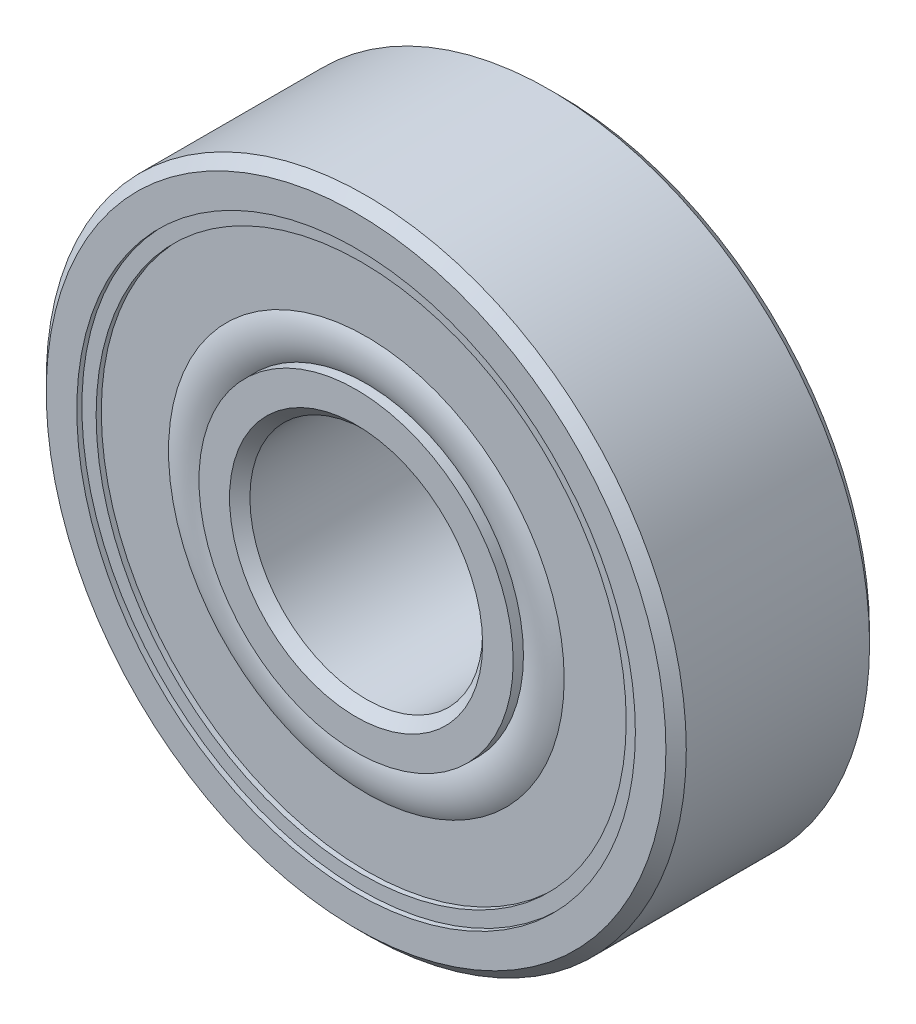
SolidWorks part; units mm, degrees
ref_plane "Front Plane" through (0, 0, 0) normal (0, 0, 1) x (1, 0, 0)
ref_plane "Top Plane" through (0, 0, 0) normal (0, 1, 0) x (1, 0, 0)
ref_plane "Right Plane" through (0, 0, 0) normal (1, 0, 0) x (0, 0, -1)
sketch "Sketch1" plane through (0, 0, 0) normal (0, 0, 1) x (1, 0, 0)
  circle A0 centre (0, 0) radius 11 construction
  circle A1 centre (0, 0) radius 4 construction
  dimension "OD" = 22
  dimension "ID" = 8
sketch "Sketch2" plane through (0, 0, 0) normal (1, 0, 0) x (0, 0, -1)
  line L0 (-3.5, 0) -> (3.5, 0) construction
  line L1 (0, 11) -> (0, -11) construction
  line L2 (3.15, 11) -> (-3.15, 11) construction
  line L3 (-3.15, 11) -> (-3.5, 10.65) construction
  line L4 (-3.5, 10.65) -> (-3.5, 9.6) construction
  line L5 (-3.5, 9.6) -> (-1.5556, 9.6) construction
  line L6 (3.5, 9.6) -> (1.5556, 9.6) construction
  line L7 (3.5, 10.65) -> (3.5, 9.6) construction
  line L8 (3.15, 11) -> (3.5, 10.65) construction
  line L9 (0, 11) -> (0, 7.5) construction
  line L10 (0, 7.5) -> (0, 4) construction
  line L11 (3.5, 7.5) -> (-3.5, 7.5) construction
  line L12 (-3.5, 4.35) -> (-3.5, 5.4) construction
  line L13 (-3.15, 4) -> (-3.5, 4.35) construction
  line L14 (3.15, 4) -> (-3.15, 4) construction
  line L15 (3.15, 4) -> (3.5, 4.35) construction
  line L16 (3.5, 4.35) -> (3.5, 5.4) construction
  line L17 (3.5, 5.4) -> (1.5556, 5.4) construction
  line L18 (-3.5, 5.4) -> (-1.5556, 5.4) construction
  line L19 (-3.5, 4) -> (-3.5, -4) construction
  line L20 (3.5, 11) -> (3.5, -11) construction
  arc A0 (-1.5556, 9.6) -> (1.5556, 9.6) centre (0, 7.5) cw construction
  arc A1 (-1.5556, 5.4) -> (1.5556, 5.4) centre (0, 7.5) ccw construction
  point P14 (0, 4)
  point P18 (0, 7.5)
  dimension "Approx. Ball Dia." = 5.2268
  dimension "D1" = 45
  dimension "D2" = 0.35
  dimension "D3" = 3.1111
  dimension "D4" = 2.1
  dimension "Width" = 7
  dimension "For Shaft Diameter" = 8
  dimension "For Housing ID" = 22
sketch "Sketch3" plane through (0, 0, 0) normal (1, 0, 0) x (0, 0, -1)
  line L0 (-3.5, 10.65) -> (-3.5, 9.6) construction
  line L1 (-3.15, 11) -> (-3.5, 10.65) construction
  line L2 (3.15, 11) -> (-3.15, 11) construction
  line L3 (3.15, 11) -> (3.5, 10.65) construction
  line L4 (3.5, 10.65) -> (3.5, 9.6) construction
  line L5 (3.5, 9.6) -> (1.5556, 9.6) construction
  line L6 (-3.5, 9.6) -> (-1.5556, 9.6) construction
  line L7 (-3.5, 10.65) -> (-3.5, 9.6)
  line L8 (-3.15, 11) -> (-3.5, 10.65)
  line L9 (3.15, 11) -> (-3.15, 11)
  line L10 (3.15, 11) -> (3.5, 10.65)
  line L11 (3.5, 10.65) -> (3.5, 9.6)
  line L12 (3.5, 9.6) -> (1.5556, 9.6)
  line L13 (-3.5, 9.6) -> (-1.5556, 9.6)
  line L14 (-3.5, 4.35) -> (-3.5, 5.4) construction
  line L15 (-3.15, 4) -> (-3.5, 4.35) construction
  line L16 (3.15, 4) -> (-3.15, 4) construction
  line L17 (3.15, 4) -> (3.5, 4.35) construction
  line L18 (3.5, 4.35) -> (3.5, 5.4) construction
  line L19 (3.5, 5.4) -> (1.5556, 5.4) construction
  line L20 (-3.5, 5.4) -> (-1.5556, 5.4) construction
  line L21 (-3.5, 4.35) -> (-3.5, 5.4)
  line L22 (-3.15, 4) -> (-3.5, 4.35)
  line L23 (3.15, 4) -> (-3.15, 4)
  line L24 (3.15, 4) -> (3.5, 4.35)
  line L25 (3.5, 4.35) -> (3.5, 5.4)
  line L26 (3.5, 5.4) -> (1.5556, 5.4)
  line L27 (-3.5, 5.4) -> (-1.5556, 5.4)
  arc A0 (1.5556, 9.6) -> (-1.5556, 9.6) centre (0, 7.5) ccw construction
  arc A1 (1.5556, 9.6) -> (-1.5556, 9.6) centre (0, 7.5) ccw
  arc A2 (-1.5556, 5.4) -> (1.5556, 5.4) centre (0, 7.5) ccw construction
  arc A3 (-1.5556, 5.4) -> (1.5556, 5.4) centre (0, 7.5) ccw
revolve "Revolve1" add sketch "Sketch3" angle 360 about L0
sketch "Sketch4" plane through (0, 0, 0) normal (1, 0, 0) x (0, 0, -1)
  line L0 (-2.6134, 7.5) -> (2.6134, 7.5)
  arc A2 (-2.6134, 7.5) -> (2.6134, 7.5) centre (0, 7.5) cw
  arc A3 (1.5556, 9.6) -> (-1.5556, 9.6) centre (0, 7.5) ccw construction
revolve "Revolve2" add sketch "Sketch4" angle 360 about L0
pattern_circular "CirPattern1" count 7 over 360 about axis through (0, 0, 0) along (0, 0, 1) of bodies 104
sketch "Sketch5" plane through (0, 0, 0) normal (1, 0, 0) x (0, 0, -1)
  line L0 (-3.5, 9.6) -> (-1.5556, 9.6) construction
  line L1 (-3.325, 9.6) -> (-2.6134, 9.6)
  line L2 (-3.325, 9.6) -> (-3.325, 9.11)
  line L3 (-3.325, 5.4) -> (-2.6134, 5.4) construction
  line L4 (-2.6134, 9.6) -> (-2.6134, 5.4)
  line L5 (0, 11) -> (0, 0) construction
  line L7 (-3.325, 9.11) -> (-3.1471, 9.11)
  line L8 (-3.1471, 9.11) -> (-3.1471, 6.8)
  line L9 (-3.1471, 6.8) -> (-3.325, 6.8) construction
  line L10 (-3.325, 6.8) -> (-3.325, 5.4) construction
  line L11 (3.15, 11) -> (-3.15, 11) construction
  line L12 (-3.15, 11) -> (-3.5, 10.65) construction
  line L13 (-3.5, 5.4) -> (-1.5556, 5.4) construction
  line L15 (-3.1471, 5.4) -> (-2.6134, 5.4)
  line L16 (3.325, 6.8) -> (3.325, 5.4) construction
  line L17 (3.1471, 6.8) -> (3.325, 6.8) construction
  line L18 (3.325, 5.4) -> (2.6134, 5.4) construction
  line L19 (3.1471, 5.4) -> (2.6134, 5.4)
  line L20 (3.1471, 9.11) -> (3.1471, 6.8)
  line L21 (3.325, 9.11) -> (3.1471, 9.11)
  line L22 (2.6134, 9.6) -> (2.6134, 5.4)
  line L23 (3.325, 9.6) -> (3.325, 9.11)
  line L24 (3.325, 9.6) -> (2.6134, 9.6)
  arc A0 (-3.1471, 5.4) -> (-3.1471, 6.8) centre (-1.8589, 6.1) cw
  arc A1 (3.1471, 5.4) -> (3.1471, 6.8) centre (1.8589, 6.1) ccw
  point P10 (-3.1471, 5.4)
  point P18 (-3.325, 10.825)
  dimension "D1" = 0.49
  dimension "D2" = 1.4
  dimension "D3" = 0.7116
  dimension "D4" = 0.1779
revolve "Revolve3" add sketch "Sketch5" angle 360 about L0
equation "\"D2@Sketch2\"= \"Width@Sketch2\" * .05"
equation "\"D3@Sketch2\"=\"Width@Sketch2\" / 2.25"
equation "\"D4@Sketch2\"=( \"OD@Sketch1\" - \"For Shaft Diameter@Sketch2\" ) *0.15"
equation "\"Approx. No. of Balls\"= ( pi * \"OD@Sketch1\" ) * .5 / \"Approx. Ball Dia.@Sketch2\""
equation "\"Balls@CirPattern1\"=\"Approx. No. of Balls\""
equation "\"D1@Sketch5\"=( \"OD@Sketch1\" - \"For Shaft Diameter@Sketch2\" ) *0.035"
equation "\"D2@Sketch5\"=( \"OD@Sketch1\" - \"For Shaft Diameter@Sketch2\" ) *0.1"
equation "\"D4@Sketch5\"=\"D3@Sketch5\"*.25"
